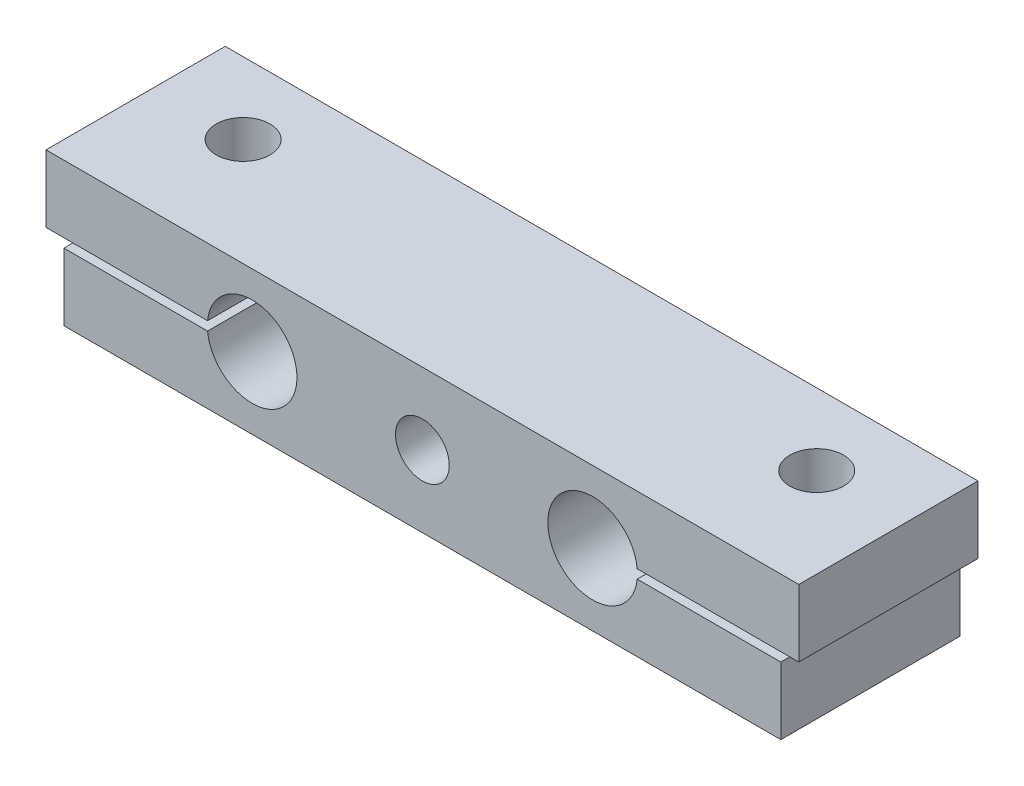
SolidWorks part; units mm, degrees
material "6061 Alloy"
ref_plane "Front Plane" through (0, 0, 0) normal (0, 0, 1) x (1, 0, 0)
ref_plane "Top Plane" through (0, 0, 0) normal (0, 1, 0) x (1, 0, 0)
ref_plane "Right Plane" through (0, 0, 0) normal (1, 0, 0) x (0, 0, -1)
sketch "Sketch1" plane through (0, 0, 0) normal (0, 0, 1) x (1, 0, 0)
  line L0 (9.4977, 0) -> (-9.4977, 0) construction
  line L1 (-19.9977, 0.25) -> (-11.9852, 0.25)
  line L2 (19.9977, -4) -> (-19.9977, -4)
  line L3 (19.9977, -4) -> (19.9977, -0.25)
  line L4 (20.0023, 4) -> (-19.9977, 4)
  line L5 (-20, -0.25) -> (-19.9977, -4)
  line L6 (19.9977, -4) -> (-19.9977, 4) construction
  line L7 (-9.4977, 0.25) -> (-9.4977, -0.25) construction
  line L8 (-11.9852, -0.25) -> (-20, -0.25)
  line L9 (19.9977, 0.25) -> (11.9852, 0.25)
  line L10 (9.4977, 0.25) -> (9.4977, -0.25) construction
  line L11 (19.9977, -0.25) -> (11.9852, -0.25)
  line L13 (-19.9977, 4) -> (-20.9977, 4)
  line L14 (20.0023, 4) -> (20.9977, 4)
  line L15 (20.9977, 4) -> (20.9977, 0.25)
  line L16 (20.9977, 0.25) -> (19.9977, 0.25)
  line L17 (-20.9977, 4) -> (-20.9977, 0.25)
  line L18 (-20.9977, 0.25) -> (-19.9977, 0.25)
  arc A0 (11.9852, 0.25) -> (11.9852, -0.25) centre (9.4977, 0) ccw
  arc A1 (-11.9852, -0.25) -> (-11.9852, 0.25) centre (-9.4977, 0) ccw
  dimension "D2" = 5
  dimension "D3" = 1
  dimension "D6" = 10.5
  dimension "D7" = 1
  dimension "D1" = 0.5
  dimension "D4" = 8
  dimension "D5" = 40
extrude "Boss-Extrude1" add sketch "Sketch1" along normal blind 10
sketch "Sketch2" plane through (0, -4, 0) normal (0, -1, 0) x (1, 0, 0)
  line L0 (-16, 4) -> (16, 4) construction
  line L1 (0, 0) -> (0, 10) construction
  line L2 (-19.9977, 0) -> (19.9977, 0) construction
  line L3 (-19.9977, 10) -> (19.9977, 10) construction
  circle A0 centre (-16, 4) radius 1.25
  circle A1 centre (16, 4) radius 1.25
  point P6 (0, 4)
  dimension "D2" = 2.5
  dimension "D1" = 32
  dimension "D3" = 4
sketch "Sketch4" plane through (0, 0, 10) normal (0, 0, 1) x (1, 0, 0)
  circle A0 centre (0, 0) radius 1.25
  dimension "D1" = 2.5
hole_wizard "M3x0.5 Tapped Hole1" positions "3DSketch1" profile "Sketch5" tap size "M3x0.5" standard "BSI"
sketch3d "3DSketch1"
  point P0 (-16, -4, 4)
  point P3 (16, -4, 4)
sketch "Sketch5" plane through (-16, -4, 4) normal (1, 0, 0) x (0, 0, -1)
  line L0 (0, 0) -> (0, 3.75)
  line L1 (0, 3.75) -> (1.25, 3.75)
  line L2 (1.25, 3.75) -> (1.25, 0)
  line L5 (1.25, 0) -> (0, 0)
  line L11 (0, -6.35) -> (0, 107.95) construction
  dimension "Thru Tap Drill Dia." = 2.5
  dimension "Thru Tap Drill Depth" = 3.75
cosmetic thread "Hole Thread1" parameters "D2"=3
cosmetic thread "Hole Thread2" parameters "D2"=3
hole_wizard "M3x0.5 Tapped Hole2" positions "3DSketch2" profile "Sketch6" tap size "M3x0.5" standard "BSI" end condition through all
sketch3d "3DSketch2"
  point P0 (0, 0, 10)
sketch "Sketch6" plane through (0, 0, 10) normal (1, 0, 0) x (0, -1, 0)
  line L0 (0, 0) -> (0, 10)
  line L1 (0, 10) -> (1.5, 10)
  line L2 (1.5, 10) -> (1.5, 0)
  line L5 (1.5, 0) -> (0, 0)
  line L11 (0, -6.35) -> (0, 107.95) construction
  dimension "Thread Major Dia." = 3
  dimension "Thru Tap Drill Depth" = 10
hole_wizard "Ø3.0mm Dowel Hole1" positions "3DSketch3" profile "Sketch8" hole size "Ø3.0" standard "BSI"
sketch3d "3DSketch3"
  line L0 (16, -0.25, 4) -> (16, -4, 4) construction
  line L1 (-16, -0.25, 4) -> (-16, -4, 4) construction
  point P0 (16, 4, 4)
  point P4 (-16, 4, 4)
sketch "Sketch8" plane through (16, 4, 4) normal (1, 0, 0) x (0, 0, 1)
  line L0 (0, 0) -> (0, 4.6503)
  line L1 (0, 4.6503) -> (1.5, 3.749)
  line L2 (1.5, 3.749) -> (1.5, 0)
  line L5 (1.5, 0) -> (0, 0)
  line L10 (0, 4.6503) -> (-1.5, 3.749) construction
  line L11 (0, -6.35) -> (0, 107.95) construction
  dimension "Hole Dia." = 3
  dimension "Hole Depth" = 3.749
  dimension "Drill Angle" = 118
